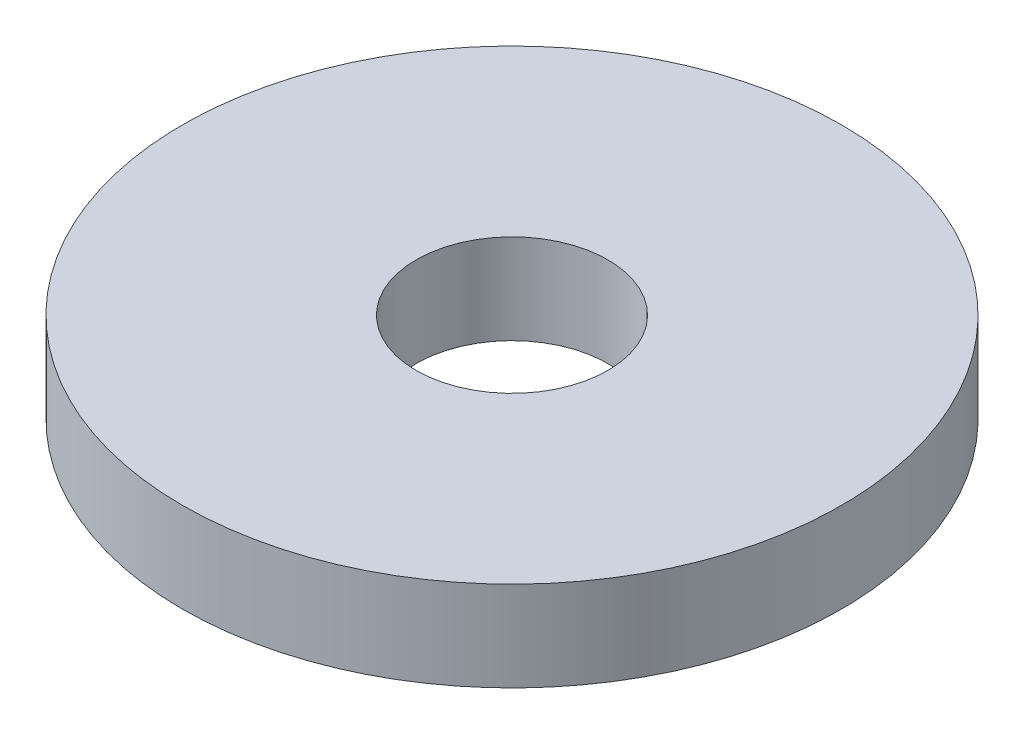
SolidWorks part; units mm, degrees
ref_plane "Alzado" through (0, 0, 0) normal (0, 0, 1) x (1, 0, 0)
ref_plane "Planta" through (0, 0, 0) normal (0, 1, 0) x (1, 0, 0)
ref_plane "Vista lateral" through (0, 0, 0) normal (1, 0, 0) x (0, 0, -1)
sketch "Croquis1" plane through (0, 0, 0) normal (0, 1, 0) x (1, 0, 0)
  circle A0 centre (0, 0) radius 3.2
  circle A1 centre (0, 0) radius 11
  dimension "D1" = 6.4
  dimension "D2" = 22
extrude "Saliente-Extruir1" add sketch "Croquis1" along normal blind 3
